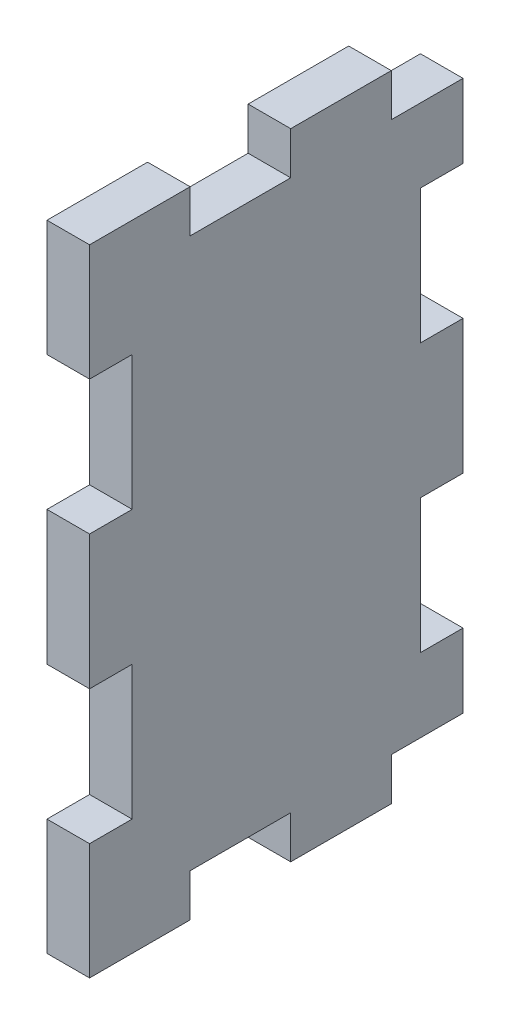
SolidWorks part; units mm, degrees
ref_plane "Front Plane" through (0, 0, 0) normal (0, 0, 1) x (1, 0, 0)
ref_plane "Top Plane" through (0, 0, 0) normal (0, 1, 0) x (1, 0, 0)
ref_plane "Right Plane" through (0, 0, 0) normal (1, 0, 0) x (0, 0, -1)
sketch "Sketch1" plane through (0, 0, 0) normal (1, 0, 0) x (0, 0, -1)
  line L1 (0, 0) -> (35.35, 0)
  line L2 (0, 0) -> (0, 47.35)
  line L3 (0, 47.35) -> (35.35, 47.35)
  line L4 (35.35, 0) -> (35.35, 47.35)
  dimension "D1" = 35.35
  dimension "D2" = 47.35
extrude "Boss-Extrude1" add sketch "Sketch1" along normal blind 3.175
sketch "Sketch2" plane through (0, 0, 0) normal (-1, 0, 0) x (0, 0, 1)
  line L0 (-35.35, 47.35) -> (0, 47.35) construction
  line L1 (-35.35, 47.35) -> (-27.85, 47.35)
  line L2 (-35.35, 47.35) -> (-35.35, 0)
  line L3 (-35.35, 0) -> (-27.85, 0)
  line L4 (-27.85, 47.35) -> (-27.85, 0)
  line L5 (-35.35, 0) -> (-35.35, 47.35) construction
  line L6 (0, 0) -> (-35.35, 0) construction
  dimension "D1" = 7.5
extrude "Cut-Extrude1" cut sketch "Sketch2" against normal through all
sketch "Sketch3" plane through (0, 0, 0) normal (-1, 0, 0) x (0, 0, 1)
  line L0 (0, 47.35) -> (0, 0) construction
  line L1 (-3.175, 8.675) -> (0, 8.675)
  line L2 (-3.175, 8.675) -> (-3.175, 18.675)
  line L3 (-3.175, 18.675) -> (0, 18.675)
  line L4 (0, 8.675) -> (0, 18.675)
  line L5 (-27.85, 0) -> (-27.85, 47.35) construction
  line L6 (-3.175, 28.675) -> (0, 28.675)
  line L7 (-3.175, 28.675) -> (-3.175, 38.675)
  line L8 (-3.175, 38.675) -> (0, 38.675)
  line L9 (0, 28.675) -> (0, 38.675)
  line L10 (-24.675, 8.675) -> (-27.85, 8.675)
  line L11 (-24.675, 8.675) -> (-24.675, 18.675)
  line L12 (-24.675, 18.675) -> (-27.85, 18.675)
  line L13 (-27.85, 8.675) -> (-27.85, 18.675)
  line L14 (-27.85, 47.35) -> (0, 47.35) construction
  line L15 (-24.675, 28.675) -> (-27.85, 28.675)
  line L16 (-24.675, 28.675) -> (-24.675, 38.675)
  line L17 (-24.675, 38.675) -> (-27.85, 38.675)
  line L18 (-27.85, 28.675) -> (-27.85, 38.675)
  line L19 (-7.5, 44.175) -> (-15, 44.175)
  line L20 (-7.5, 44.175) -> (-7.5, 47.35)
  line L21 (-7.5, 47.35) -> (-15, 47.35)
  line L22 (-15, 44.175) -> (-15, 47.35)
  line L23 (0, 0) -> (-27.85, 0) construction
  line L24 (-7.5, 3.175) -> (-15, 3.175)
  line L25 (-7.5, 3.175) -> (-7.5, 0)
  line L26 (-7.5, 0) -> (-15, 0)
  line L27 (-15, 3.175) -> (-15, 0)
  line L28 (-27.85, 0) -> (-27.85, 47.35) construction
  line L29 (-22.5, 44.175) -> (-27.85, 44.175)
  line L30 (-22.5, 44.175) -> (-22.5, 47.35)
  line L31 (-22.5, 47.35) -> (-27.85, 47.35)
  line L32 (-27.85, 44.175) -> (-27.85, 47.35)
  line L34 (-22.5, 3.175) -> (-27.85, 3.175)
  line L35 (-22.5, 3.175) -> (-22.5, 0)
  line L36 (-22.5, 0) -> (-27.85, 0)
  line L37 (-27.85, 3.175) -> (-27.85, 0)
  dimension "D1" = 7.5
  dimension "D2" = 7.5
  dimension "D3" = 7.5
  dimension "D4" = 3.175
  dimension "D5" = 10
  dimension "D6" = 10
  dimension "D7" = 8.675
  dimension "D8" = 3.175
extrude "Cut-Extrude2" cut sketch "Sketch3" against normal through all
